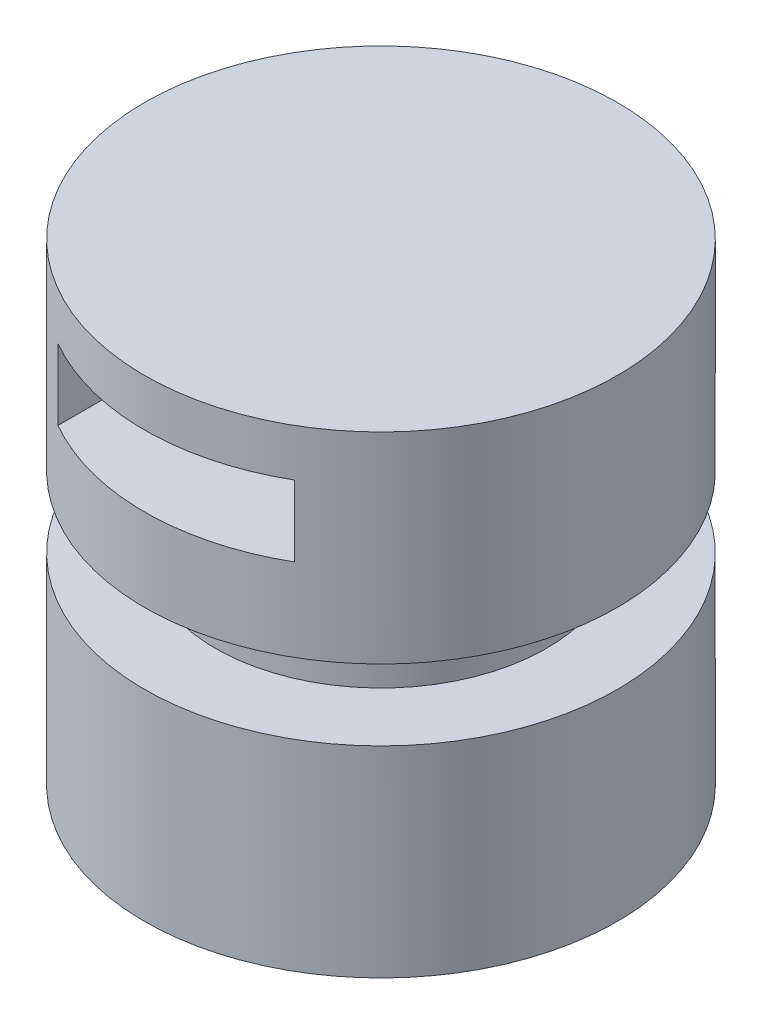
SolidWorks part; units mm, degrees
ref_plane "Front Plane" through (0, 0, 0) normal (0, 0, 1) x (1, 0, 0)
ref_plane "Top Plane" through (0, 0, 0) normal (0, 1, 0) x (1, 0, 0)
ref_plane "Right Plane" through (0, 0, 0) normal (1, 0, 0) x (0, 0, -1)
sketch "Sketch1" plane through (0, 0, 0) normal (0, 0, 1) x (1, 0, 0)
  line L1 (0, 200) -> (100, 200)
  line L2 (0, 200) -> (0, 0)
  line L3 (0, 0) -> (100, 0)
  line L4 (100, 200) -> (100, 0)
  dimension "D1" = 100
  dimension "D2" = 200
revolve "Revolve1" add sketch "Sketch1" angle 360 about L2
sketch "Sketch3" plane through (0, 0, 0) normal (1, 0, 0) x (0, 0, -1)
  line L1 (70, 115) -> (100, 115)
  line L2 (70, 115) -> (70, 85)
  line L3 (70, 85) -> (100, 85)
  line L4 (100, 115) -> (100, 85)
  line L5 (0, 0) -> (0, 200) construction
  line L6 (100, 200) -> (-100, 200) construction
  line L7 (100, 0) -> (100, 200) construction
  line L9 (70, 100) -> (100, 100) construction
  dimension "D1" = 30
  dimension "D2" = 100
revolve "Cut-Revolve1" cut sketch "Sketch3" angle 360 about L5
sketch "Sketch4" plane through (0, 0, 0) normal (0, 0, 1) x (1, 0, 0)
  line L0 (0, 200) -> (0, 0) construction
  line L1 (100, 200) -> (-100, 200) construction
  line L3 (-50, 180) -> (50, 180)
  line L4 (-50, 180) -> (-50, 150)
  line L5 (-50, 150) -> (50, 150)
  line L6 (50, 180) -> (50, 150)
  point P9 (0, 180)
  dimension "D1" = 100
  dimension "D2" = 30
  dimension "D3" = 20
extrude "Cut-Extrude1" cut sketch "Sketch4" against normal through all both and the other way through all
